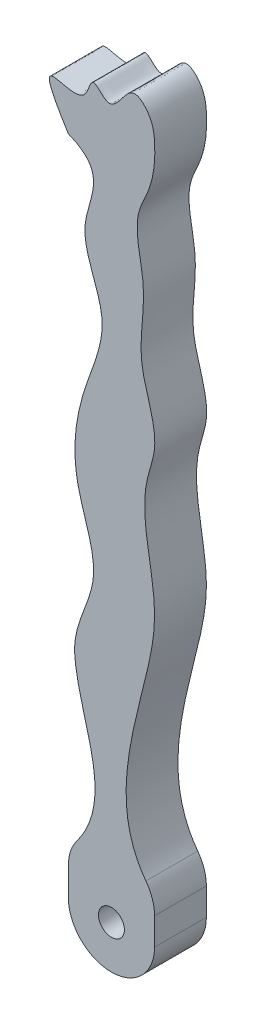
SolidWorks part; units mm, degrees
ref_plane "Front Plane" through (0, 0, 0) normal (0, 0, 1) x (1, 0, 0)
ref_plane "Top Plane" through (0, 0, 0) normal (0, 1, 0) x (1, 0, 0)
ref_plane "Right Plane" through (0, 0, 0) normal (1, 0, 0) x (0, 0, -1)
sketch "Sketch1" plane through (0, 0, 0) normal (0, 0, 1) x (1, 0, 0)
  line L0 (4.99, 0) -> (4.99, -9.98) construction
  line L2 (0, 0) -> (0, -9.98)
  line L3 (0, -9.98) -> (9.98, -9.98)
  line L4 (9.98, 0) -> (9.98, -9.98)
  circle A0 centre (4.99, -4.99) radius 1.5
  spline S0 degree 3 poles (0, 54.2507) (-1.3002, 57.7322) (3.2647, 54.3642) (2.4263, 59.6713) (6.2497, 57.9313) (7.56, 60.3083) (10.809, 60.4277) (10.3371, 56.9019) (8.6679, 54.3949) (7.6248, 50.0404) (9.268, 44.5549) (7.0461, 37.9736) (9.8469, 30.217) (6.2703, 21.6733) (10.7937, 11.1069) (4.4749, 3.4165) (9.98, 0) knots 0 0 0 0 0.053422 0.084053 0.123826 0.153488 0.181182 0.220513 0.254556 0.310198 0.388256 0.476668 0.57334 0.700293 0.819187 1 1 1 1
  spline S1 degree 3 poles (0, 54.2507) (5.0844, 51.6989) (-1.0405, 45.9919) (5.4473, 39.8872) (0.9091, 34.169) (6.0054, 27.5034) (0.487, 20.0549) (5.6717, 12.8445) (0.4035, 6.2112) (5.1771, 1.3503) (0, 0) knots 0 0 0 0 0.175025 0.26981 0.365352 0.476782 0.633954 0.755983 0.862891 1 1 1 1
  dimension "D3" = 3
  dimension "D1" = 9.98
  dimension "D2" = 9.98
extrude "Boss-Extrude1" add sketch "Sketch1" along normal blind 6
sketch "Sketch2" plane through (0, 0, 6) normal (0, 0, 1) x (1, 0, 0)
  line L1 (-3.1937, -4.99) -> (16.0799, -4.99)
  line L2 (-3.1937, -4.99) -> (-3.1937, -13.2025)
  line L3 (-3.1937, -13.2025) -> (16.0799, -13.2025)
  line L4 (16.0799, -4.99) -> (16.0799, -13.2025)
  circle A0 centre (4.99, -4.99) radius 4.99
sketch "Sketch3" plane through (0, 0, 0) normal (-1, 0, 0) x (0, 0, 1)
  line L1 (0, 0) -> (6, 0)
  line L2 (0, 0) -> (0, 60.2717)
  line L3 (0, 60.2717) -> (6, 60.2717)
  line L4 (6, 0) -> (6, 60.2717)
  line L5 (0, 0) -> (6, 0)
  line L6 (0, 0) -> (0, 80)
  line L7 (0, 80) -> (6, 80)
  line L8 (6, 0) -> (6, 80)
  line M9 (6, 0) -> (0, 0)
  dimension "D1" = 60.2717
  dimension "D2" = 80
extrude "Boss-Extrude2" add sketch "Sketch3" against normal blind 10 contours L3 L8 L7 L6 | L4 L3 L2 M9
sketch "Sketch4" plane through (0, 0, 0) normal (0, -1, 0) x (1, 0, 0)
  line L1 (9.98, 6) -> (19.0311, 6)
  line L2 (9.98, 6) -> (9.98, 0)
  line L3 (9.98, 0) -> (19.0311, 0)
  line L4 (19.0311, 6) -> (19.0311, 0)
extrude "Cut-Extrude1" cut sketch "Sketch4" against normal blind 162
sketch "Sketch5" plane through (0, -9.98, 0) normal (0, -1, 0) x (1, 0, 0)
  line L1 (0, 6) -> (-2.7768, 6)
  line L2 (0, 6) -> (0, -1.674)
  line L3 (0, -1.674) -> (-2.7768, -1.674)
  line L4 (-2.7768, 6) -> (-2.7768, -1.674)
extrude "Cut-Extrude2" cut sketch "Sketch5" against normal blind 162
sketch "Sketch6" plane through (0, 0, 6) normal (0, 0, 1) x (1, 0, 0)
  line L0 (0, 80) -> (0, -9.98) construction
  line L1 (9.98, -9.98) -> (9.98, 80) construction
  line L2 (0, 0) -> (9.98, 0)
  spline S0 degree 3 poles (0, 71.565) (-5.2335, 79.9076) (1.7686, 73.0949) (2.6703, 79.1569) (5.223, 75.3266) (6.9563, 80.7794) (9.7238, 77.9961) (10.1601, 74.896) (9.8448, 71.2011) (7.1889, 66.6374) (9.4932, 60.3692) (7.4709, 52.8018) (10.8926, 46.3283) (7.6795, 38.4278) (10.9608, 30.1274) (7.842, 16.604) (4.6225, 5.4014) (9.98, 0) knots 0 0 0 0 0.074805 0.094366 0.114748 0.154561 0.178597 0.202324 0.25557 0.288548 0.360702 0.443388 0.525057 0.564586 0.697374 0.776283 1 1 1 1
  spline S1 degree 3 poles (0, 71.565) (4.9538, 69.5879) (-0.3493, 63.4928) (5.4675, 55.1456) (1.2724, 46.575) (-0.0166, 37.4764) (4.5091, 28.7823) (0.375, 22.6223) (1.4889, 12.7256) (5.6361, 6.0312) (0, 0) knots 0 0 0 0 0.126259 0.23872 0.351182 0.484025 0.603345 0.708763 0.749079 1 1 1 1
extrude "Boss-Extrude5" add sketch "Sketch6" against normal blind 6
sketch "Sketch8" plane through (0, 0, 0) normal (0, 0, 1) x (1, 0, 0)
  line L3 (0, 0) -> (9.98, 0)
  line L4 (0, 0) -> (0, 80)
  line L5 (0, 80) -> (9.98, 80)
  line L6 (9.98, 0) -> (9.98, 80)
  spline S0 degree 3 poles (0, 71.565) (-5.2335, 79.9076) (1.7686, 73.0949) (2.6703, 79.1569) (5.223, 75.3266) (6.9563, 80.7794) (9.7238, 77.9961) (10.1601, 74.896) (9.8448, 71.2011) (7.1889, 66.6374) (9.4932, 60.3692) (7.4709, 52.8018) (10.8926, 46.3283) (7.6795, 38.4278) (10.9608, 30.1274) (7.842, 16.604) (4.6225, 5.4014) (9.98, 0) knots 0 0 0 0 0.074805 0.094366 0.114748 0.154561 0.178597 0.202324 0.25557 0.288548 0.360702 0.443388 0.525057 0.564586 0.697374 0.776283 1 1 1 1
  spline S1 degree 3 poles (0, 71.565) (4.9538, 69.5879) (-0.3493, 63.4928) (5.4675, 55.1456) (1.2724, 46.575) (-0.0166, 37.4764) (4.5091, 28.7823) (0.375, 22.6223) (1.4889, 12.7256) (5.6361, 6.0312) (0, 0) knots 0 0 0 0 0.126259 0.23872 0.351182 0.484025 0.603345 0.708763 0.749079 1 1 1 1
extrude "Cut-Extrude6" cut sketch "Sketch8" along normal blind 6 contours L6 S0 | S1 L4 | L6 S0 | L6 S0 | L4 S0 L6 L5
sketch "Sketch9" plane through (0, 0, 6) normal (0, 0, 1) x (1, 0, 0)
  line L1 (9.98, -9.98) -> (0, -9.98)
  line L2 (9.98, -9.98) -> (9.98, 0)
  line L3 (9.98, 0) -> (0, 0)
  line L4 (0, -9.98) -> (0, 0)
  circle A0 centre (4.99, -4.99) radius 4.99
  line M3 (0, -9.98) -> (9.98, -9.98)
  line M4 (9.98, -9.98) -> (9.98, 0)
extrude "Cut-Extrude7" cut sketch "Sketch9" against normal blind 6 contours A0 L4 M3 | A0 L1 M4
fillet "Fillet1" radius 5 2 edges at (9.98, 0, 3) (0, 0, 3)
